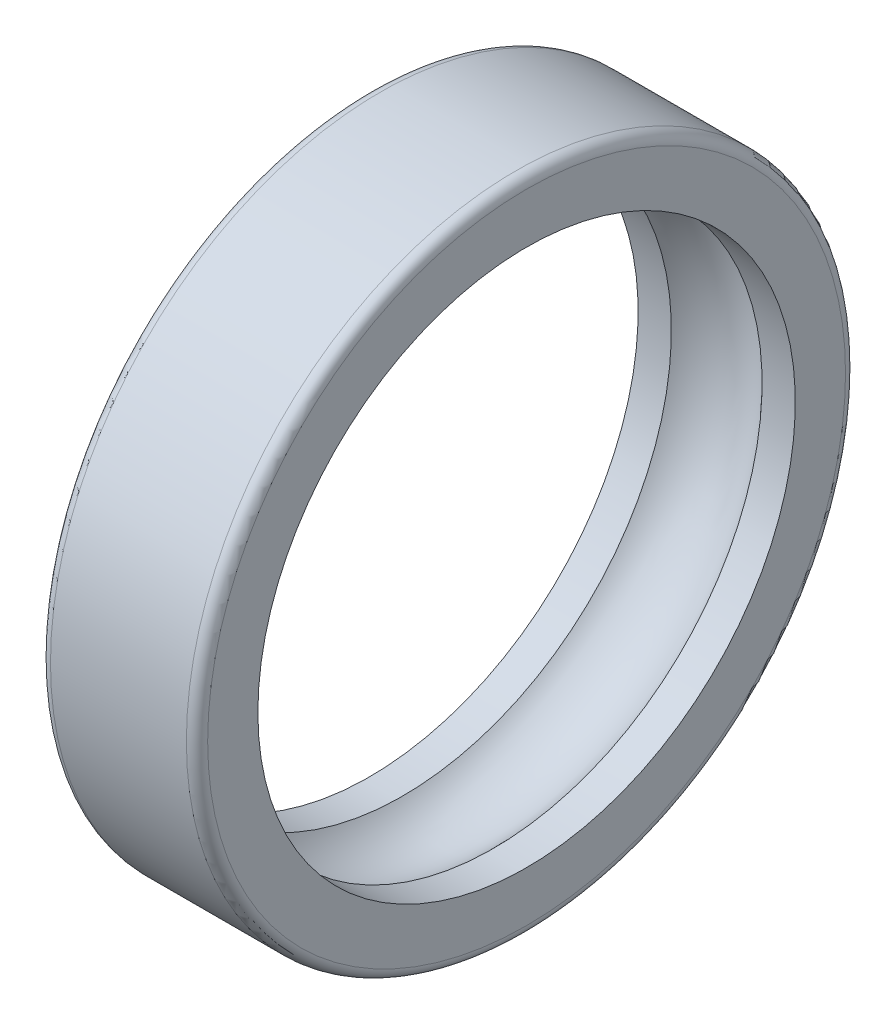
SolidWorks part; units mm, degrees
ref_plane "Front Plane" through (0, 0, 0) normal (0, 0, 1) x (1, 0, 0)
ref_plane "Top Plane" through (0, 0, 0) normal (0, 1, 0) x (1, 0, 0)
ref_plane "Right Plane" through (0, 0, 0) normal (1, 0, 0) x (0, 0, -1)
sketch "Sketch1" plane through (0, 0, 0) normal (0, 0, 1) x (1, 0, 0)
  line L0 (-9.3928, 0) -> (42.9553, 0) construction
  line L1 (0, 53) -> (0, 0) construction
  line L2 (-15.5, 65) -> (15.5, 65)
  line L3 (-15.5, 65) -> (-15.5, 53)
  line L4 (-15.5, 53) -> (-8.9443, 53)
  line L5 (15.5, 65) -> (15.5, 53)
  line L6 (-15.5, 65) -> (15.5, 53) construction
  line L7 (-15.5, 53) -> (15.5, 65) construction
  line L8 (8.9443, 53) -> (15.5, 53)
  arc A0 (-8.9443, 53) -> (8.9443, 53) centre (0, 45) cw
  point P3 (0, 59)
  dimension "D5" = 12
  dimension "D1" = 31
  dimension "D2" = 53
  dimension "D3" = 65
  dimension "D4" = 8
revolve "Revolve1" add sketch "Sketch1" angle 360 about L0
fillet "Fillet1" radius 2.1 2 edges at (15.5, 0, 65) (-15.5, 0, 65)
